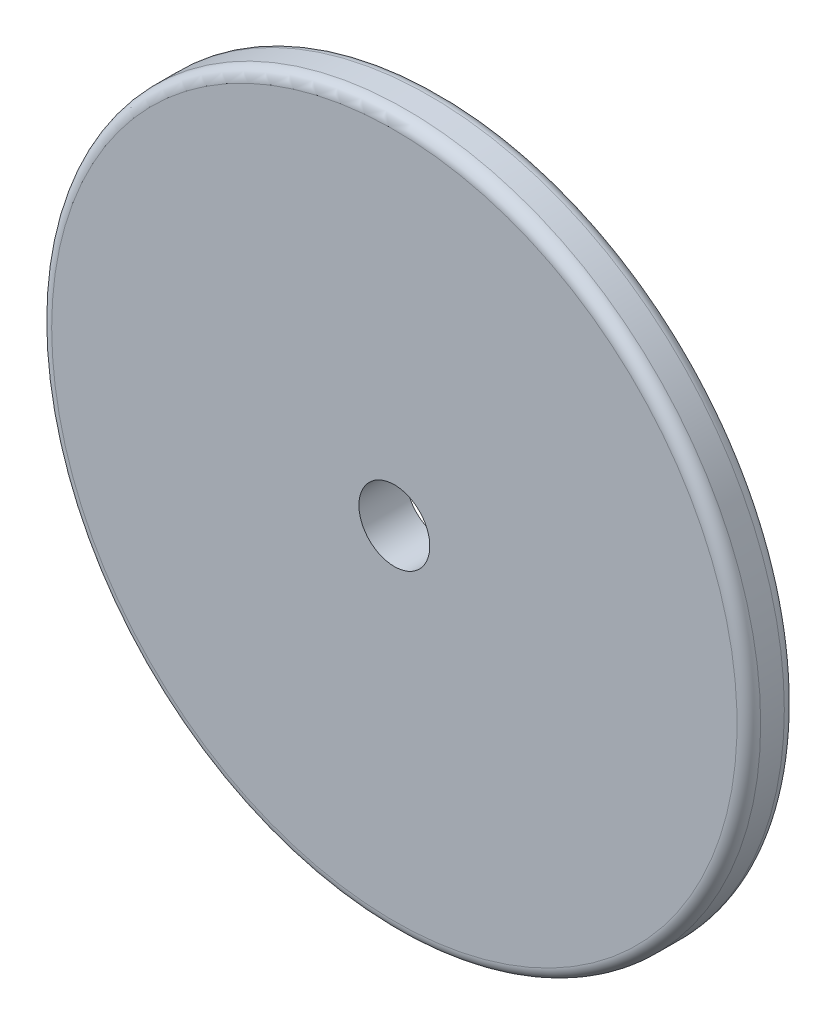
SolidWorks part; units mm, degrees
ref_plane "Front Plane" through (0, 0, 0) normal (0, 0, 1) x (1, 0, 0)
ref_plane "Top Plane" through (0, 0, 0) normal (0, 1, 0) x (1, 0, 0)
ref_plane "Right Plane" through (0, 0, 0) normal (1, 0, 0) x (0, 0, -1)
ref_plane "Plane1" through (-0.0071, -0.0031, 41.8971) normal (0.0002, 0.0001, -1) x (0.8372, 0.5469, 0.0002)
sketch "Sketch2" plane through (-0.0071, -0.0031, 41.8971) normal (0.0002, 0.0001, -1) x (0.8372, 0.5469, 0.0002)
  circle A0 centre (-55.822, 127.3048) radius 15
  circle A1 centre (-55.822, 127.3048) radius 1.5
  dimension "D1" = 30
  dimension "D2" = 3
extrude "Boss-Extrude1" add sketch "Sketch2" along normal blind 2
fillet "Fillet1" radius 0.5 1 edges at (7.889, -137.1102, 41.8884)
fillet "Fillet3" radius 0.5 1 edges at (7.8893, -137.1101, 39.8884)
